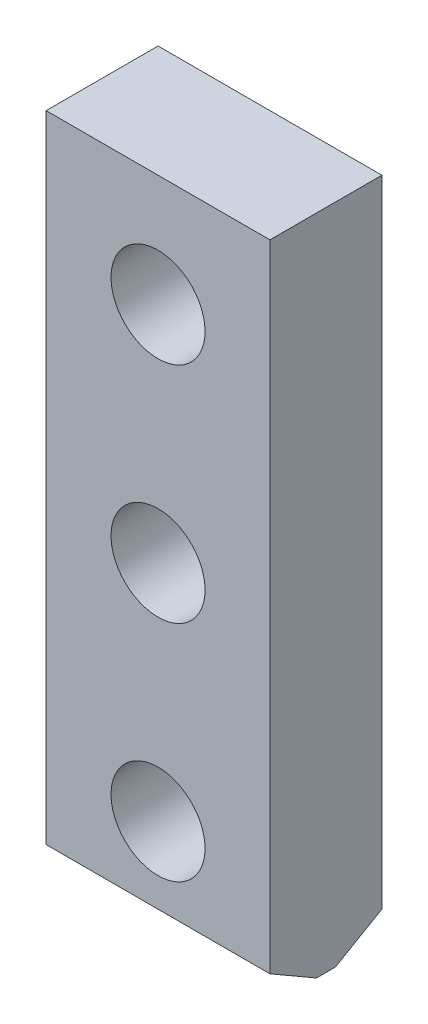
SolidWorks part; units mm, degrees
material "Простая углеродистая сталь"
ref_plane "Спереди" through (0, 0, 0) normal (0, 0, 1) x (1, 0, 0)
ref_plane "Сверху" through (0, 0, 0) normal (0, 1, 0) x (1, 0, 0)
ref_plane "Справа" through (0, 0, 0) normal (1, 0, 0) x (0, 0, -1)
sketch "Эскиз1" plane through (0, 0, 0) normal (0, 0, 1) x (1, 0, 0)
  line L1 (0, 0) -> (50, 0)
  line L2 (0, 0) -> (0, 148)
  line L3 (0, 148) -> (50, 148)
  line L4 (50, 0) -> (50, 148)
  point P5 (25, 148)
  dimension "D1" = 148
  dimension "D2" = 50
extrude "Бобышка-Вытянуть1" add sketch "Эскиз1" along normal blind 25
sketch "Эскиз2" plane through (0, 0, 25) normal (0, 0, 1) x (1, 0, 0)
  line L0 (0, 0) -> (50, 0) construction
  line L1 (50, 0) -> (50, 148) construction
  circle A0 centre (25, 23) radius 10.5
  circle A1 centre (25, 73) radius 10.5
  circle A2 centre (25, 123) radius 10.5
  dimension "D1" = 3
  dimension "D2" = 23
  dimension "D3" = 25
  dimension "D4" = 21
extrude "Вырез-Вытянуть1" cut sketch "Эскиз2" against normal through all
chamfer "Фаска1" distance 6 angle 60 1 edges at (25, 0, 0)
chamfer "Фаска2" distance 6 angle 60 1 edges at (25, 0, 25)
